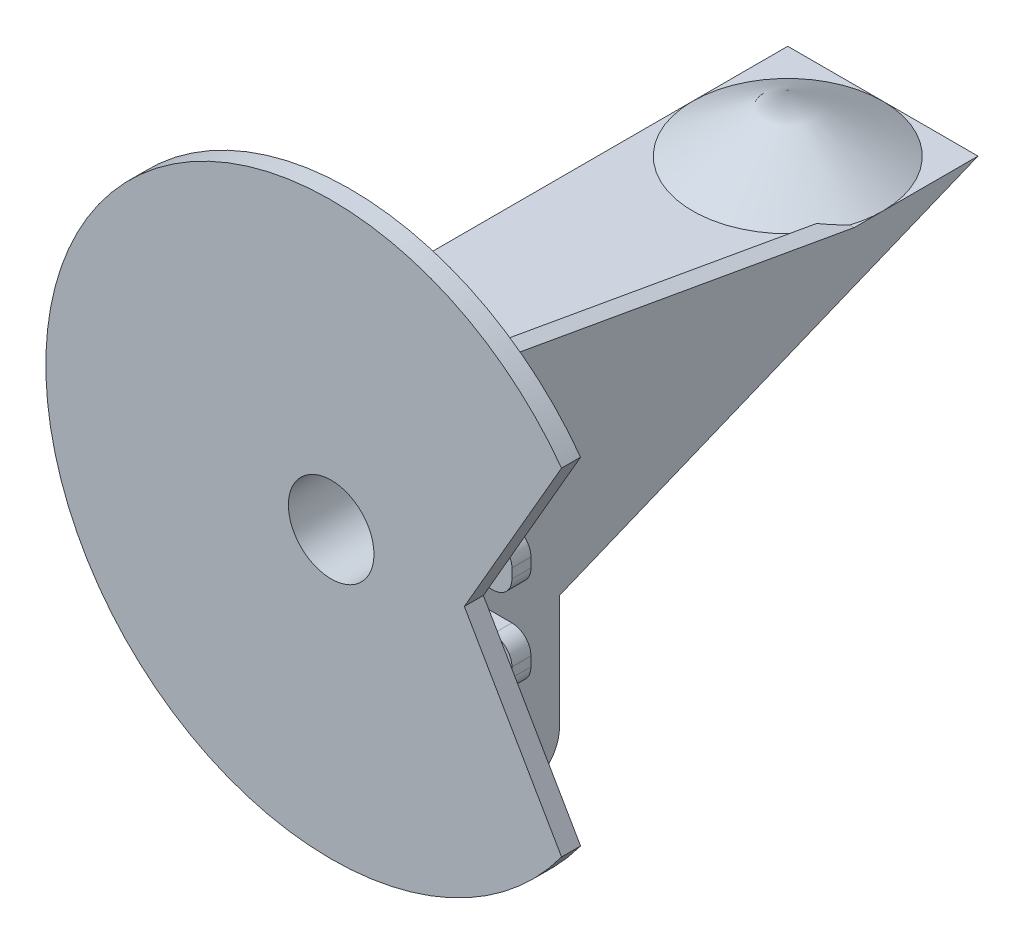
SolidWorks part; units mm, degrees
ref_plane "Płaszczyzna przednia" through (0, 0, 0) normal (0, 0, 1) x (1, 0, 0)
ref_plane "Płaszczyzna górna" through (0, 0, 0) normal (0, 1, 0) x (1, 0, 0)
ref_plane "Płaszczyzna prawa" through (0, 0, 0) normal (1, 0, 0) x (0, 0, -1)
sketch "Szkic1" plane through (0, 0, 0) normal (0, 0, 1) x (1, 0, 0)
  line L1 (-50, 50) -> (50, 50)
  line L2 (-50, 50) -> (-50, -50)
  line L3 (-50, -50) -> (50, -50)
  line L4 (50, 50) -> (50, -50)
  line L5 (-50, 50) -> (50, -50) construction
  line L6 (-50, -50) -> (50, 50) construction
  point P0 (0, 0)
  dimension "D1" = 100
extrude "Dodanie-wyciągnięcie1" add sketch "Szkic1" along normal blind 40
sketch "Szkic3" plane through (0, 0, 40) normal (0, 0, 1) x (1, 0, 0)
  circle A0 centre (0, 0) radius 22.5
  dimension "D1" = 45
extrude "Wytnij-wyciągnięcie1" cut sketch "Szkic3" against normal through all
sketch "Szkic4" plane through (0, 0, 0) normal (0, 0, -1) x (-1, 0, 0)
  line L0 (50, 50) -> (50, -50) construction
  line L1 (-50, -50) -> (50, -50)
  line L2 (-50, -50) -> (-50, -40)
  line L3 (-50, -40) -> (50, -40)
  line L4 (50, -50) -> (50, -40)
  dimension "D1" = 10
extrude "Dodanie-wyciągnięcie2" add sketch "Szkic4" along normal blind 30
sketch "Szkic5" plane through (-50, 0, 0) normal (-1, 0, 0) x (0, 0, 1)
  line L0 (-30, -40) -> (-250, 50)
  line L1 (-250, 50) -> (0, 50)
  line L2 (-30, -40) -> (0, -40) construction
  line L3 (0, 50) -> (0, -40) construction
  line L4 (-30, -40) -> (0, -40)
  line L5 (0, 50) -> (0, -40)
  dimension "D1" = 250
extrude "Dodanie-wyciągnięcie3" add sketch "Szkic5" against normal blind 10 contours L0 L1 L5 L4
sketch "Szkic6" plane through (50, 0, 0) normal (1, 0, 0) x (0, 0, -1)
  line L10 (30, -40) -> (250, 50)
  line L11 (250, 50) -> (0, 50)
  line L12 (0, 50) -> (0, -40)
  line L13 (0, -40) -> (30, -40)
  line L14 (30, -40) -> (250, 50)
  line L15 (250, 50) -> (0, 50)
  line L16 (0, 50) -> (0, -40)
  line L17 (0, -40) -> (30, -40)
  dimension "D1" = 0
extrude "Dodanie-wyciągnięcie4" add sketch "Szkic6" against normal blind 10
sketch "Szkic7" plane through (0, 50, 0) normal (0, 1, 0) x (1, 0, 0)
  line L0 (-40, 250) -> (40, 250)
  line L1 (-40, 250) -> (-40, 0) construction
  line L2 (-40, 30) -> (-40, 0) construction
  line L3 (40, 0) -> (-40, 0) construction
  line L5 (-40, 250) -> (-40, 0)
  line L6 (-40, 30) -> (-40, 0)
  line L7 (40, 0) -> (-40, 0)
  line L8 (40, 250) -> (40, 0) construction
  line L9 (40, 250) -> (40, 0)
extrude "Dodanie-wyciągnięcie5" add sketch "Szkic7" against normal blind 10
ref_plane "Płaszczyzna1" through (0, 0, -200) normal (0, 0, -1) x (-1, 0, 0)
sketch "Szkic10" plane through (0, 0, -200) normal (0, 0, -1) x (-1, 0, 0)
  line L0 (0, 50) -> (0, 80)
  line L1 (40, 50) -> (-40, 50) construction
  line L2 (0, 80) -> (-50, 50)
  line L3 (-50, 50) -> (0, 50)
  dimension "D1" = 30
revolve "Obrót1" add sketch "Szkic10" angle 360 about L0
sketch "Szkic11" plane through (0, -50, 0) normal (0, -1, 0) x (1, 0, 0)
  line L5 (50, 40) -> (50, -30) construction
  line L6 (50, 20) -> (35, 20)
  line L7 (50, 20) -> (50, -30)
  line L8 (50, -30) -> (35, -30)
  line L9 (35, 20) -> (35, -30)
  line L10 (50, -30) -> (-50, -30) construction
  dimension "D1" = 50
  dimension "D2" = 15
extrude "Dodanie-wyciągnięcie6" add sketch "Szkic11" along normal blind 70
sketch "Szkic12" plane through (35, 0, 0) normal (-1, 0, 0) x (0, 0, 1)
  line L0 (20, -120) -> (-30, -120) construction
  line L1 (20, -120) -> (20, -50) construction
  circle A0 centre (-5, -85) radius 15
  dimension "D1" = 30
  dimension "D2" = 35
  dimension "D3" = 25
extrude "Dodanie-wyciągnięcie7" add sketch "Szkic12" along normal blind 125
sketch "Szkic13" plane through (-50, 0, 0) normal (-1, 0, 0) x (0, 0, 1)
  circle A0 centre (-40, 0) radius 15
  dimension "D1" = 30
  dimension "D2" = 40
extrude "Dodanie-wyciągnięcie8" add sketch "Szkic13" along normal blind 30
ref_plane "Płaszczyzna2" through (-60, 0, 0) normal (-1, 0, 0) x (0, 0, 1)
sketch "Szkic14" plane through (-60, 0, 0) normal (-1, 0, 0) x (0, 0, 1)
  line L0 (20, -120) -> (-30, -120) construction
  line L1 (-69.0109, 20.0371) -> (-26.9998, 36.1636)
  line L2 (-69.0109, 20.0371) -> (-15.2557, -120)
  line L3 (-15.2557, -120) -> (26.7554, -103.8734)
  line L4 (-26.9998, 36.1636) -> (26.7554, -103.8734)
  line L5 (-30, -120) -> (-30, -50) construction
  circle A3 centre (-5, -85) radius 15 construction
  dimension "D2" = 159
  dimension "D4" = 29
  dimension "D1" = 150
  dimension "D3" = 45
extrude "Dodanie-wyciągnięcie9" add sketch "Szkic14" along normal blind 10
fillet "Zaokrąglenie1" radius 20 6 edges at (42.5, -120, 20) (42.5, -120, -30) (-65, 36.1636, -26.9998) (-65, 20.0371, -69.0109) (-65, -103.8734, 26.7554) (-65, -120, -15.2557)
sketch "Szkic15" plane through (-90, 0, 0) normal (-1, 0, 0) x (0, 0, 1)
  line L0 (0, -120) -> (-10, -120) construction
  line L1 (-30, 65) -> (20, 65)
  line L2 (-30, 65) -> (-30, -120)
  line L3 (-30, -120) -> (20, -120)
  line L4 (20, 65) -> (20, -120)
  line L5 (20, -100) -> (20, -50) construction
  line L6 (-30, -100) -> (-30, -50) construction
  dimension "D1" = 185
sketch "Szkic17" plane through (-50, 0, 0) normal (-1, 0, 0) x (0, 0, 1)
  line L0 (-30, 65) -> (-30, -120) construction
  line L1 (-30, 65) -> (20, 65)
  line L2 (-30, 65) -> (-30, 35)
  line L3 (-30, 35) -> (20, 35)
  line L4 (20, 65) -> (20, 35)
  line L6 (20, 65) -> (20, -120) construction
  line L9 (-30, 65) -> (20, 65) construction
  dimension "D1" = 30
extrude "Dodanie-wyciągnięcie10" add sketch "Szkic15" along normal blind 10 contours L1 L4 L3 L2
extrude "Dodanie-wyciągnięcie11" add sketch "Szkic17" along normal up to next contours L1 L4 L3 L2
sketch "Szkic18" plane through (0, 0, 40) normal (0, 0, 1) x (1, 0, 0)
  line L0 (121.1021, 88.5115) -> (70, 0)
  line L1 (70, 0) -> (121.1021, -88.5115)
  line L2 (50, -50) -> (50, 50) construction
  circle A0 centre (0, 0) radius 150
  line M4 (50, -50) -> (50, 50)
  line M5 (50, 50) -> (-50, 50)
  line M6 (-50, 50) -> (-50, -50)
  line M7 (-50, -50) -> (50, -50)
  dimension "D1" = 300
  dimension "D2" = 70
  dimension "D3" = 120
  dimension "D4" = 30
extrude "Dodanie-wyciągnięcie12" add sketch "Szkic18" against normal blind 10 contours L0 A0 L1 M4 M7 M6 M5
sketch "Szkic19" plane through (50, 0, 0) normal (1, 0, 0) x (0, 0, -1)
  line L0 (-30, 50) -> (-9.9586, 84.6171)
  line L1 (-9.9586, 84.6171) -> (185, 50)
  line L2 (-30, 50) -> (200, 50) construction
  line L3 (185, 50) -> (-30, 50)
  dimension "D1" = 65
  dimension "D2" = 40
  dimension "D3" = 110
extrude "Dodanie-wyciągnięcie13" add sketch "Szkic19" against normal blind 10 contours L1 L3 L0
sketch "Szkic20" plane through (50, 0, 0) normal (1, 0, 0) x (0, 0, -1)
  circle A0 centre (-4.9586, 69.6171) radius 5
  dimension "D1" = 10
  dimension "D2" = 15
  dimension "D3" = 5
extrude "Wytnij-wyciągnięcie2" cut sketch "Szkic20" against normal up to next
sketch "Szkic21" plane through (50, 0, 0) normal (1, 0, 0) x (0, 0, -1)
  line L1 (-20, -50) -> (-10, -50)
  line L2 (-20, -50) -> (-20, 20)
  line L3 (-20, 20) -> (-10, 20)
  line L4 (-10, -50) -> (-10, 20)
  line L5 (-20, -5) -> (-10, -5)
  line L6 (-20, -5) -> (-20, -25)
  line L7 (-20, -25) -> (-10, -25)
  line L8 (-10, -5) -> (-10, -25)
  point P9 (-15, -50)
  dimension "D1" = 70
  dimension "D2" = 10
  dimension "D3" = 25
  dimension "D4" = 25
extrude "Dodanie-wyciągnięcie14" add sketch "Szkic21" along normal blind 25 contours L2 L5 L4 L3 | L7 L2 L1 L4
fillet "Zaokrąglenie2" radius 10 5 edges at (75, -50, 15) (75, -25, 15) (75, -5, 15) (75, 20, 15) (45, 84.6171, 9.9586)
sketch "Szkic22" plane through (0, 0, 10) normal (0, 0, -1) x (-1, 0, 0)
  line L0 (-75, 5) -> (-75, 10) construction
  circle A0 centre (-63, 7.5) radius 5
  circle A1 centre (-63, -37.5) radius 5
  dimension "D1" = 12
  dimension "D2" = 10
  dimension "D4" = 10
  dimension "D3" = 2.5
  dimension "D5" = 2.5
extrude "Wytnij-wyciągnięcie3" cut sketch "Szkic22" against normal up to next
